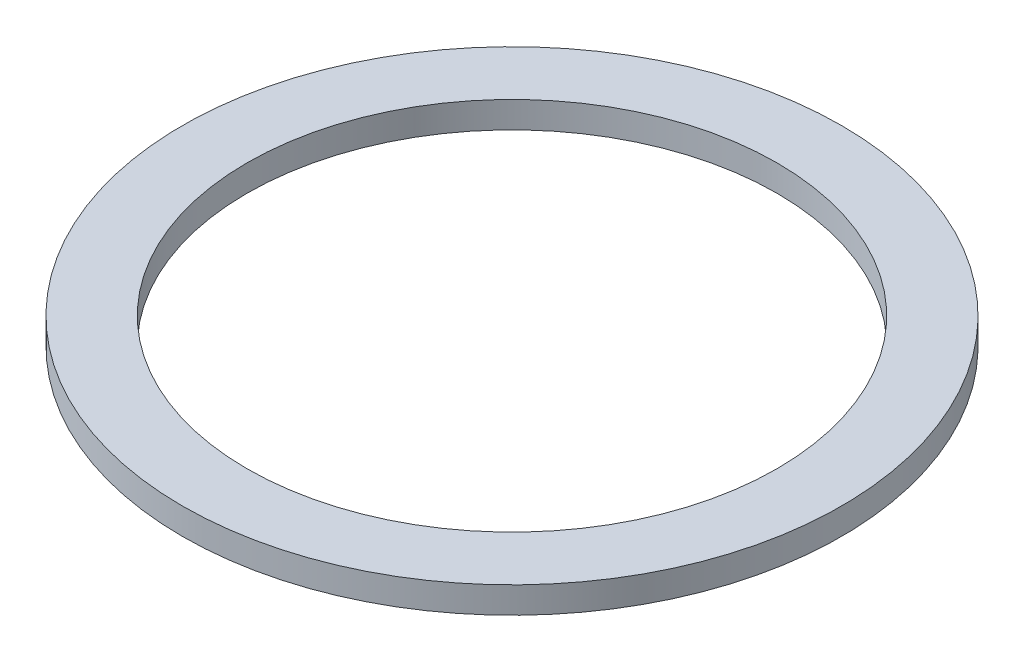
SolidWorks part; units mm, degrees
ref_plane "Front Plane" through (0, 0, 0) normal (0, 0, 1) x (1, 0, 0)
ref_plane "Top Plane" through (0, 0, 0) normal (0, 1, 0) x (1, 0, 0)
ref_plane "Right Plane" through (0, 0, 0) normal (1, 0, 0) x (0, 0, -1)
sketch "Sketch1" plane through (0, 0, 0) normal (0, 1, 0) x (1, 0, 0)
  circle A0 centre (0, 0) radius 12.5
  circle A1 centre (0, 0) radius 10.05
extrude "Boss-Extrude1" add sketch "Sketch1" along normal blind 1
